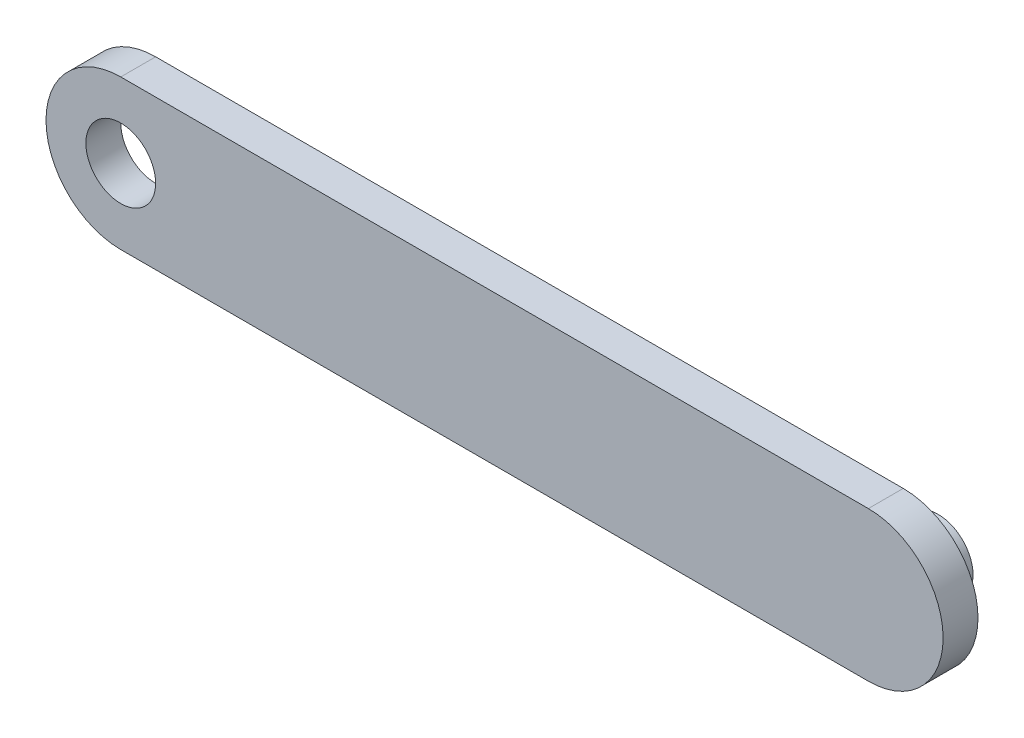
SolidWorks part; units mm, degrees
ref_plane "Front Plane" through (0, 0, 0) normal (0, 0, 1) x (1, 0, 0)
ref_plane "Top Plane" through (0, 0, 0) normal (0, 1, 0) x (1, 0, 0)
ref_plane "Right Plane" through (0, 0, 0) normal (1, 0, 0) x (0, 0, -1)
sketch "Sketch1" plane through (0, 0, 0) normal (0, 0, 1) x (1, 0, 0)
  line L0 (-75, 0) -> (75, 0) construction
  line L1 (-75, 15) -> (75, 15)
  line L2 (-75, -15) -> (75, -15)
  arc A0 (-75, 15) -> (-75, -15) centre (-75, 0) ccw
  arc A1 (75, -15) -> (75, 15) centre (75, 0) ccw
  point P2 (0, 0)
  dimension "D1" = 150
  dimension "D2" = 30
extrude "Boss-Extrude1" add sketch "Sketch1" along normal blind 7
sketch "Sketch2" plane through (0, 0, 0) normal (0, 0, 1) x (1, 0, 0)
  line L0 (75, 15) -> (75, -15) construction
  line L1 (90, 0) -> (-90, 0) construction
  line L2 (-75, 15) -> (-75, -15) construction
  arc A0 (75, -15) -> (75, 15) centre (75, 0) ccw construction
  arc A1 (-75, 15) -> (-75, -15) centre (-75, 0) ccw construction
  circle A2 centre (75, 0) radius 7
  dimension "D1" = 14
extrude "Boss-Extrude3" add sketch "Sketch2" against normal blind 7
sketch "Sketch3" plane through (0, 0, 0) normal (0, 0, -1) x (-1, 0, 0)
  line L0 (75, 15) -> (75, -15) construction
  line L1 (90, 0) -> (0, 0) construction
  arc A0 (75, -15) -> (75, 15) centre (75, 0) ccw construction
  circle A1 centre (75, 0) radius 7
  dimension "D1" = 14
extrude "Cut-Extrude1" cut sketch "Sketch3" against normal blind 7
